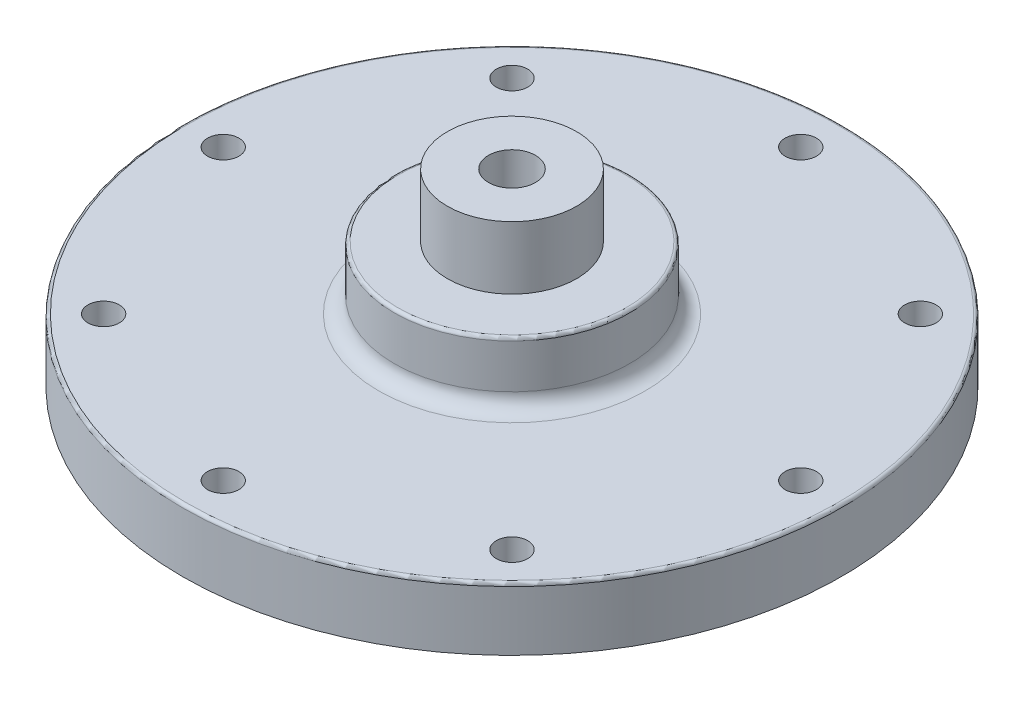
SolidWorks part; units mm, degrees
ref_plane "Front Plane" through (0, 0, 0) normal (0, 0, 1) x (1, 0, 0)
ref_plane "Top Plane" through (0, 0, 0) normal (0, 1, 0) x (1, 0, 0)
ref_plane "Right Plane" through (0, 0, 0) normal (1, 0, 0) x (0, 0, -1)
sketch "Sketch1" plane through (0, 0, 0) normal (0, 1, 0) x (1, 0, 0)
  circle A0 centre (0, 0) radius 66.675
  dimension "D1" = 133.35
extrude "Flange" add sketch "Sketch1" along normal blind 12.7
sketch "Sketch for Bolt Holes" plane through (0, 12.7, 0) normal (0, 1, 0) x (1, 0, 0)
  circle A0 centre (0, 0) radius 58.42
  circle A1 centre (0, 58.42) radius 3.175
  circle A2 centre (41.3092, 41.3092) radius 3.175
  circle A3 centre (58.42, 0) radius 3.175
  circle A4 centre (41.3092, -41.3092) radius 3.175
  circle A5 centre (0, -58.42) radius 3.175
  circle A6 centre (-41.3092, -41.3092) radius 3.175
  circle A7 centre (-58.42, 0) radius 3.175
  circle A8 centre (-41.3092, 41.3092) radius 3.175
  point P21 (0, 0)
  dimension "D1" = 6.35
  dimension "D2" = 8
hole_wizard "Bolt Holes" positions "Sketch4" profile "Sketch5" hole size "1/4" standard "ANSI Inch" end condition up to next
sketch "Sketch4" plane through (0, 12.7, 0) normal (0, 1, 0) x (1, 0, 0)
  point P0 (41.3092, -41.3092)
  point P3 (0, -58.42)
  point P6 (-41.3092, -41.3092)
  point P9 (-58.42, 0)
  point P12 (-41.3092, 41.3092)
  point P15 (0, 58.42)
  point P18 (41.3092, 41.3092)
  point P21 (58.42, 0)
sketch "Sketch5" plane through (41.3092, 12.7, 41.3092) normal (1, 0, 0) x (0, 0, 1)
  line L0 (0, 0) -> (0, 12.7)
  line L1 (0, 12.7) -> (3.175, 12.7)
  line L2 (3.175, 12.7) -> (3.175, 0)
  line L5 (3.175, 0) -> (0, 0)
  line L11 (0, -6.35) -> (0, 107.95) construction
  dimension "Thru Hole Dia." = 6.35
  dimension "Thru Hole Depth" = 12.7
sketch "Sketch for Pin Holes" plane through (0, 0, 0) normal (0, -1, 0) x (1, 0, 0)
  line L0 (0, 58.42) -> (0, 0) construction
  line L1 (-22.3564, 53.973) -> (0, 0) construction
  circle A0 centre (0, 0) radius 58.42
  circle A1 centre (-22.3564, 53.973) radius 2.6883
  circle A2 centre (22.3564, -53.973) radius 2.6883
  point P12 (0, 0)
  dimension "D1" = 22.5
  dimension "D2" = 2
hole_wizard "Pin Holes" positions "Sketch9" profile "Sketch10" hole size "1/4" standard "ANSI Inch"
sketch "Sketch9" plane through (0, 0, 0) normal (0, -1, 0) x (-1, 0, 0)
  point P0 (22.3564, -53.973)
  point P3 (-22.3564, 53.973)
sketch "Sketch10" plane through (-22.3564, 0, 53.973) normal (1, 0, 0) x (0, 0, -1)
  line L0 (0, 0) -> (0, 8.2577)
  line L1 (0, 8.2577) -> (3.175, 6.35)
  line L2 (3.175, 6.35) -> (3.175, 0)
  line L5 (3.175, 0) -> (0, 0)
  line L10 (0, 8.2577) -> (-3.175, 6.35) construction
  line L11 (0, -6.35) -> (0, 107.95) construction
  dimension "Hole Dia." = 6.35
  dimension "Hole Depth" = 6.35
  dimension "Drill Angle" = 118
sketch "Sketch2" plane through (0, 12.7, 0) normal (0, 1, 0) x (1, 0, 0)
  circle A0 centre (0, 0) radius 23.8125
  circle A1 centre (0, 0) radius 12.7
  dimension "D1" = 47.625
  dimension "D2" = 25.4
extrude "Flow Extrude" add sketch "Sketch2" along normal blind 12.7
sketch "Sketch6" plane through (0, 25.4, 0) normal (0, 1, 0) x (1, 0, 0)
  circle A0 centre (0, 0) radius 4.7625
  circle A1 centre (0, 0) radius 13.081
  dimension "D1" = 9.525
  dimension "D2" = 26.162
extrude "Nitrous Connection Flange" add sketch "Sketch6" along normal blind 12.7
cosmetic thread "Cosmetic Thread2" parameters "D2"=23.1953
sketch "Sketch12" plane through (0, 0, 0) normal (0, -1, 0) x (1, 0, 0)
  circle A0 centre (0, 0) radius 23.8125
  dimension "D1" = 47.625
extrude "Initial Entry - Impinging Plate" cut sketch "Sketch12" against normal blind 5.715
ref_plane "Impinging Plate Forward/Top Plane" through (0, 6.35, 0) normal (0, -1, 0) x (-1, 0, 0)
sketch "Sketch14" plane through (0, 6.35, 0) normal (0, -1, 0) x (-1, 0, 0)
  circle A0 centre (0, 0) radius 23.749
  dimension "D1" = 47.498
sketch "Sketch15" plane through (0, 5.715, 0) normal (0, -1, 0) x (1, 0, 0)
  circle A1 centre (0, 0) radius 23.8125
  circle A2 centre (0, 0) radius 23.8125
  dimension "D1" = 0
loft "Impinging Plate Press Fit Cut" cut profiles "Sketch14", "Sketch15"
sketch "Sketch16" plane through (0, 6.35, 0) normal (0, -1, 0) x (1, 0, 0)
  circle A0 centre (0, 0) radius 12.7
  dimension "D1" = 25.4
extrude "Final Flow Cut" cut sketch "Sketch16" against normal blind 6.35
sketch "Sketch for Impinging Screws" plane through (0, 6.35, 0) normal (0, -1, 0) x (1, 0, 0)
  circle A0 centre (0, 0) radius 17.4625
  circle A7 centre (0, -17.4625) radius 2.1001
  circle A8 centre (-17.4625, 0) radius 2.1001
  circle A9 centre (0, 17.4625) radius 2.1001
  circle A10 centre (17.4625, 0) radius 2.1001
  point P14 (0, 0)
  point P18 (0, 0)
  dimension "D1" = 34.925
  dimension "D2" = 4
hole_wizard "Tap Holes for Impinging Plate" positions "Sketch19" profile "Sketch20" hole size "#10-24" standard "ANSI Inch"
sketch "Sketch19" plane through (0, 6.35, 0) normal (0, -1, 0) x (-1, 0, 0)
  point P0 (0, 17.4625)
  point P3 (17.4625, 0)
  point P6 (0, -17.4625)
  point P9 (-17.4625, 0)
sketch "Sketch20" plane through (0, 6.35, -17.4625) normal (1, 0, 0) x (0, 0, -1)
  line L0 (0, 0) -> (0, 13.8408)
  line L1 (0, 13.8408) -> (1.8986, 12.7)
  line L2 (1.8986, 12.7) -> (1.8986, 0)
  line L5 (1.8986, 0) -> (0, 0)
  line L10 (0, 13.8408) -> (-1.8987, 12.7) construction
  line L11 (0, -6.35) -> (0, 107.95) construction
  dimension "Hole Dia." = 3.7973
  dimension "Hole Depth" = 12.7
  dimension "Drill Angle" = 118
fillet "Flow Extrude Fillet" radius 3.175 1 edges at (0, 12.7, 23.8125)
fillet "Final Fillet for Handling" radius 0.635 2 edges at (0, 25.4, 23.8125) (0, 12.7, 66.675)
